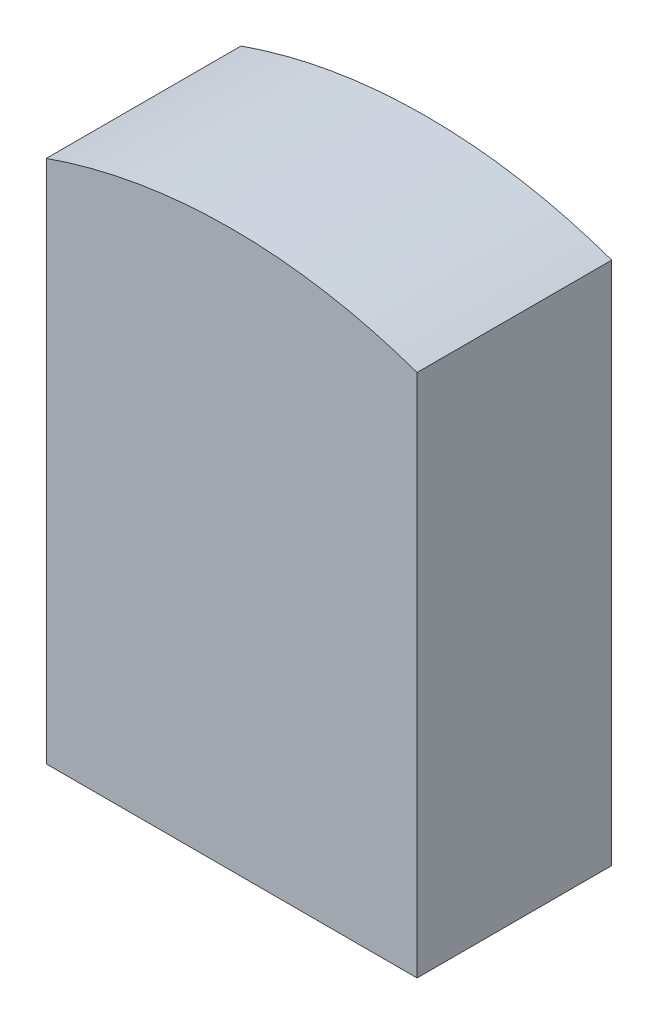
SolidWorks part; units mm, degrees
ref_plane "Plan de face" through (0, 0, 0) normal (0, 0, 1) x (1, 0, 0)
ref_plane "Plan de dessus" through (0, 0, 0) normal (0, 1, 0) x (1, 0, 0)
ref_plane "Plan de droite" through (0, 0, 0) normal (1, 0, 0) x (0, 0, -1)
sketch "Esquisse2" plane through (0, 0, 0) normal (0, 0, 1) x (1, 0, 0)
  line L0 (8.4503, -169.1228) -> (141.7837, -169.1228)
  line L1 (8.4503, -169.1228) -> (8.4503, 19.439)
  line L2 (141.7837, -169.1228) -> (141.7837, 19.439)
  arc A0 (141.7837, 19.439) -> (8.4503, 19.439) centre (75.117, -169.1228) ccw
  point P5 (141.7837, -169.1228)
  point P8 (8.4503, -169.1228)
extrude "Boss.-Extru.3" add sketch "Esquisse2" along normal blind 70
